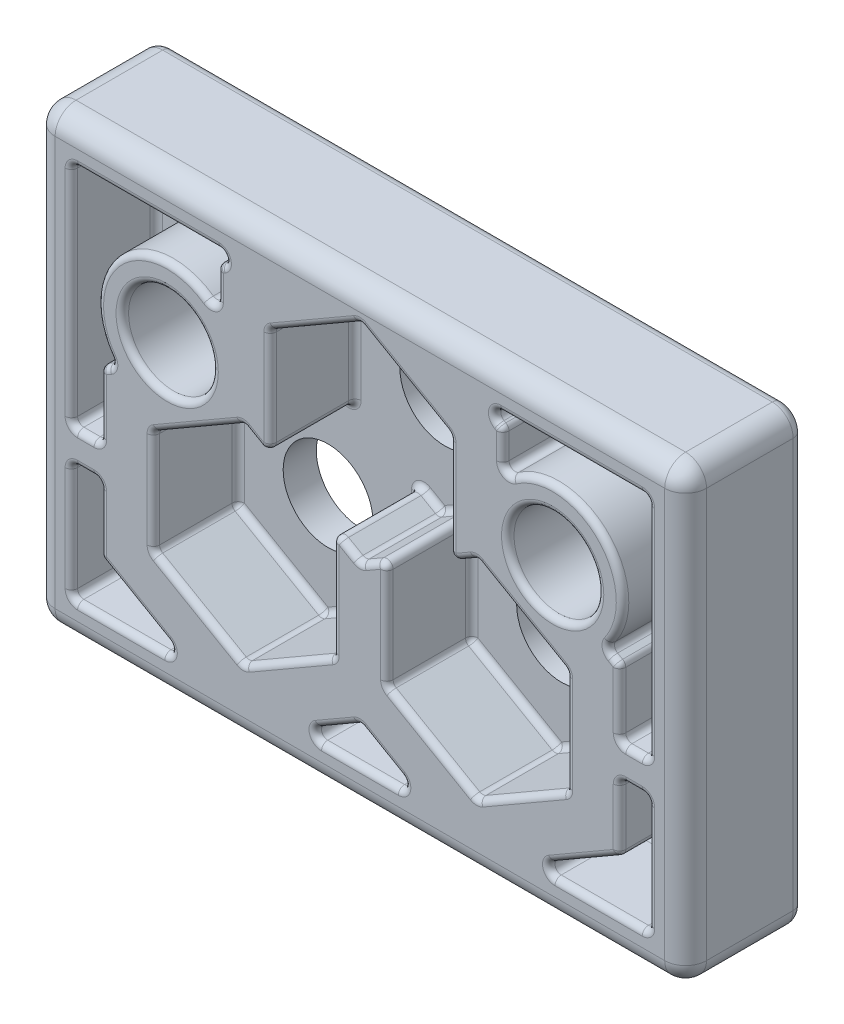
SolidWorks part; units mm, degrees
ref_plane "Front Plane" through (0, 0, 0) normal (0, 0, 1) x (1, 0, 0)
ref_plane "Top Plane" through (0, 0, 0) normal (0, 1, 0) x (1, 0, 0)
ref_plane "Right Plane" through (0, 0, 0) normal (1, 0, 0) x (0, 0, -1)
sketch "Sketch1" plane through (0, 0, 0) normal (0, 0, 1) x (1, 0, 0)
  line L0 (0, 10.795) -> (0, -10.795) construction
  line L1 (-15.5956, 10.795) -> (15.5956, 10.795)
  line L2 (-15.5956, 10.795) -> (-15.5956, -10.795)
  line L3 (-15.5956, -10.795) -> (15.5956, -10.795)
  line L4 (15.5956, 10.795) -> (15.5956, -10.795)
  line L5 (-15.5956, 10.795) -> (15.5956, -10.795) construction
  line L6 (-15.5956, -10.795) -> (15.5956, 10.795) construction
  line L7 (-5.5905, -2.6391) -> (5.5905, -2.6391) construction
  line L8 (-9.2291, 3.9218) -> (9.2291, 3.9218) construction
  circle A0 centre (0, 4.3713) radius 2.1488
  circle A1 centre (5.5905, -2.6391) radius 2.1488
  circle A2 centre (-5.5905, -2.6391) radius 2.1488
  circle A3 centre (-9.2291, 3.9218) radius 2.1488
  circle A4 centre (9.2291, 3.9218) radius 2.1488
  point P0 (0, 0)
  point P13 (0, -2.6391)
  point P17 (0, 3.9218)
  point P19 (0, 0)
  dimension "D6" = 4.2977
  dimension "D1" = 31.1912
  dimension "D2" = 21.59
  dimension "D3" = 8.1559
  dimension "D4" = 11.1811
  dimension "D5" = 6.4237
  dimension "D7" = 18.4582
  dimension "D8" = 6.8732
extrude "Boss-Extrude1" add sketch "Sketch1" along normal blind 5.6515
sketch "Sketch2" plane through (0, 0, 5.6515) normal (0, 0, 1) x (1, 0, 0)
  line L0 (-2.957, -9.017) -> (0, -7.3098)
  line L1 (-5.5905, -7.6045) -> (-1.2903, -5.1218)
  line L2 (-1.2903, -2.6391) -> (-1.2903, -0.1563)
  line L3 (-1.2903, -0.1563) -> (-5.5905, 2.3264)
  line L5 (-5.5905, 2.3264) -> (-9.8908, -0.1563)
  line L6 (-9.8908, -0.1563) -> (-9.8908, -5.1218)
  line L7 (-9.8908, -5.1218) -> (-5.5905, -7.6045)
  line L8 (0, -0.5941) -> (4.3002, 1.8886)
  line L9 (4.3002, 1.8886) -> (4.3002, 6.8541)
  line L10 (4.3002, 6.8541) -> (0, 9.3368)
  line L11 (0, 9.3368) -> (-4.3002, 6.8541)
  line L12 (-4.3002, 6.8541) -> (-4.3002, 1.8886)
  line L13 (-4.3002, 1.8886) -> (0, -0.5941)
  line L14 (5.5905, -7.6045) -> (9.8908, -5.1218)
  line L15 (9.8908, -5.1218) -> (9.8908, -0.1563)
  line L16 (9.8908, -0.1563) -> (5.5905, 2.3264)
  line L53 (5.5905, 2.3264) -> (1.2903, -0.1563)
  line L54 (1.2903, -0.1563) -> (1.2903, -5.1218)
  line L55 (1.2903, -5.1218) -> (5.5905, -7.6045)
  line L59 (-12.4308, 1.3101) -> (-12.4308, -6.5883)
  line L60 (-12.4308, -6.5883) -> (-8.2241, -9.017)
  line L61 (1.2903, -2.7821) -> (1.2927, -2.7808)
  line L63 (6.8402, 8.3205) -> (0, 12.2697)
  line L64 (0, 12.2697) -> (-6.8402, 8.3205)
  line L69 (-6.8402, 8.3205) -> (-6.8402, 6.2671)
  line L71 (8.2241, -9.017) -> (12.4308, -6.5883)
  line L72 (12.4308, -6.5883) -> (12.4308, 1.3101)
  line L73 (12.4308, 1.3101) -> (11.7408, 1.7085)
  line L74 (4.3002, 4.5144) -> (4.2979, 4.513)
  line L76 (0, -7.3098) -> (2.957, -9.017)
  line L77 (-4.3002, 1.8886) -> (-4.3002, 1.5814)
  line L78 (-1.2903, -0.1563) -> (-1.2903, 0.1508)
  line L79 (-1.2903, 0.1508) -> (-4.3002, 1.8886)
  line L80 (-4.3002, 1.5814) -> (-1.2903, -0.1563)
  line L81 (1.2903, -0.1563) -> (1.2903, 0.1508)
  line L82 (1.2903, 0.1508) -> (4.3002, 1.8886)
  line L83 (4.3002, 1.5814) -> (1.2903, -0.1563)
  line L84 (4.3002, 1.8886) -> (4.3002, 1.5814)
  line L85 (-13.8176, -1.8771) -> (-12.4308, -1.8771)
  line L86 (-13.8176, 9.017) -> (13.8176, 9.017)
  line L87 (-13.8176, 9.017) -> (-13.8176, -9.017)
  line L88 (-13.8176, -9.017) -> (-8.2241, -9.017)
  line L89 (13.8176, 9.017) -> (13.8176, -9.017)
  line L90 (-13.8176, 9.017) -> (-5.8761, 3.8346) construction
  line L91 (-13.8176, -9.017) -> (5.8824, 3.8387) construction
  line L92 (-12.4308, -1.8771) -> (-12.4308, -3.4011)
  line L93 (-12.4308, -3.4011) -> (-13.8176, -3.4011)
  line L94 (-13.8176, -3.4011) -> (-13.8176, -1.8771)
  line L95 (12.4308, -1.8771) -> (13.8176, -1.8771)
  line L96 (13.8176, -1.8771) -> (13.8176, -3.4011)
  line L97 (13.8176, -3.4011) -> (12.4308, -3.4011)
  line L98 (12.4308, -3.4011) -> (12.4308, -1.8771)
  line L99 (0, -3.5271) -> (6.8402, 0.4221) construction
  line L100 (12.4308, 1.3101) -> (5.5905, 5.2593) construction
  line L101 (6.8402, 6.2671) -> (6.8402, 8.3205)
  line L102 (6.8402, 0.4221) -> (6.8402, 8.3205) construction
  line L104 (5.8824, 3.8387) -> (13.8176, 9.017) construction
  line L105 (5.5905, -10.5375) -> (12.4308, -6.5883) construction
  line L106 (-1.2497, -6.5883) -> (5.5905, -10.5375) construction
  line L107 (8.2241, -9.017) -> (13.8176, -9.017)
  line L108 (-5.5905, -10.5375) -> (1.2497, -6.5883) construction
  line L109 (-12.4308, -6.5883) -> (-5.5905, -10.5375) construction
  line L110 (-2.957, -9.017) -> (2.957, -9.017)
  line L111 (-1.2497, 1.3101) -> (-1.2497, -6.5883) construction
  line L112 (1.2497, -6.5883) -> (1.2497, 1.3101) construction
  line L113 (-1.2903, -5.1218) -> (-1.2903, -2.6391)
  line L114 (-6.8402, 0.4221) -> (0, -3.5271) construction
  line L115 (-6.8402, 8.3205) -> (-6.8402, 0.4221) construction
  line L116 (-11.7408, 1.7085) -> (-12.4308, 1.3101)
  line L117 (-5.5905, 5.2593) -> (-12.4308, 1.3101) construction
  line L119 (1.2497, 1.3101) -> (-5.5905, 5.2593) construction
  line L120 (-5.8761, 3.8346) -> (13.8176, -9.017) construction
  line L121 (5.5905, 5.2593) -> (-1.2497, 1.3101) construction
  line L123 (-1.2903, -5.1218) -> (-1.2903, -0.1563) construction
  circle A0 centre (-5.5905, -2.6391) radius 4.3002 construction
  circle A1 centre (0, 4.3713) radius 4.3002 construction
  circle A2 centre (5.5905, -2.6391) radius 4.3002 construction
  circle A8 centre (-9.2291, 3.9218) radius 3.3477
  arc A9 (-6.8402, 6.2671) -> (-11.7408, 1.7085) centre (-9.2291, 3.9218) ccw
  circle A11 centre (9.2291, 3.9218) radius 3.3477
  arc A12 (11.7408, 1.7085) -> (6.8402, 6.2671) centre (9.2291, 3.9218) ccw
  point P31 (-2.0869, -0.1501)
  point P40 (-1.4822, -5.1155)
  point P46 (0, 0)
  point P49 (0, 0)
  point P60 (0, 0)
  point P69 (-1.4014, -1.668)
  point P72 (-1.2903, -2.5892)
  point P75 (-1.2903, -2.6391)
  point P83 (-5.8192, 3.9218)
  point P84 (-4.3002, -0.5941)
  dimension "D1" = 2.54
  dimension "D6" = 5.6159
  dimension "D7" = 1.1989
  dimension "D8" = 1.1989
  dimension "D2" = 8.6004
  dimension "D3" = 27.6352
  dimension "D4" = 18.034
  dimension "D5" = 1.524
extrude "Cut-Extrude3" cut sketch "Sketch2" against normal blind 4.064
fillet "Fillet1" radius 0.2997 114 edges at (-13.1242, -3.4011, 5.6515) (-11.0208, -9.017, 5.6515) (-1.4785, -8.1634, 5.6515) (1.4785, -8.1634, 5.6515) (13.8176, -6.209, 5.6515) (12.4308, -4.9947, 5.6515) (11.0208, -9.017, 5.6515) (9.7258, 9.017, 5.6515) (6.8402, 7.2938, 5.6515) (-4.3002, 4.2178, 5.6515) (2.1501, 8.0954, 5.6515) (4.9454, 1.9539, 5.6515) (9.8908, -2.6391, 5.6515) (3.4404, -6.3632, 5.6515) (0.6452, -0.2216, 5.6515) (-1.2903, -2.4855, 5.6515) (-7.7406, -6.3632, 5.6515) (-7.7406, 1.085, 5.6515) (-9.7258, 9.017, 5.6515) (-13.1242, -1.8771, 5.6515) (-12.0858, 1.5093, 5.6515) (-6.8402, 7.2938, 5.6515) (-8.2241, -9.017, 3.6195) (-10.3274, -7.8026, 5.6515) (-12.4308, -6.5883, 3.6195) (-12.4308, -3.4011, 3.6195) (-12.4308, -4.9947, 5.6515) (-13.8176, -3.4011, 3.6195) (-13.8176, -6.209, 5.6515) (-10.3274, -7.8026, 1.5875) (-11.0208, -9.017, 1.5875) (-13.8176, -6.209, 1.5875) (-13.1242, -3.4011, 1.5875) (-12.4308, -4.9947, 1.5875) (-2.957, -9.017, 3.6195) (2.957, -9.017, 3.6195) (0, -9.017, 5.6515) (1.4785, -8.1634, 1.5875) (0, -9.017, 1.5875) (-1.4785, -8.1634, 1.5875) (13.8176, -3.4011, 3.6195) (12.4308, -3.4011, 3.6195) (13.1242, -3.4011, 5.6515) (12.4308, -6.5883, 3.6195) (8.2241, -9.017, 3.6195) (12.4308, -4.9947, 1.5875) (13.1242, -3.4011, 1.5875) (13.8176, -6.209, 1.5875) (11.0208, -9.017, 1.5875) (10.3274, -7.8026, 1.5875) (12.4308, 1.3101, 3.6195) (12.4308, -0.2835, 5.6515) (13.8176, -1.8771, 3.6195) (13.8176, 9.017, 3.6195) (13.8176, 3.57, 5.6515) (6.8402, 8.3205, 3.6195) (6.8402, 7.2938, 1.5875) (9.7258, 9.017, 1.5875) (13.8176, 3.57, 1.5875) (13.1242, -1.8771, 1.5875) (12.4308, -0.2835, 1.5875) (12.0858, 1.5093, 1.5875) (6.8402, 6.2671, 3.6195) (11.5092, 6.3729, 1.5875) (11.7408, 1.7085, 3.6195) (11.5092, 6.3729, 5.6515) (-2.1501, 8.0954, 1.5875) (-2.1501, 8.0954, 5.6515) (4.3002, 1.5814, 3.6195) (4.3002, 6.8541, 3.6195) (4.3002, 4.2178, 5.6515) (9.8908, -0.1563, 3.6195) (7.7406, 1.085, 1.5875) (5.5905, 2.3264, 3.6195) (7.7406, 1.085, 5.6515) (9.8908, -5.1218, 3.6195) (1.2903, 0.1508, 3.6195) (1.2903, -2.4855, 1.5875) (1.2903, -5.1218, 3.6195) (1.2903, -2.4855, 5.6515) (-1.2903, 0.1508, 3.6195) (0, -0.5941, 3.6195) (-5.5905, -7.6045, 3.6195) (-3.4404, -6.3632, 1.5875) (-1.2903, -5.1218, 3.6195) (-3.4404, -6.3632, 5.6515) (-9.8908, -2.6391, 1.5875) (-9.8908, -5.1218, 3.6195) (-9.8908, -2.6391, 5.6515) (-4.3002, 1.5814, 3.6195) (-4.9454, 1.9539, 1.5875) (-5.5905, 2.3264, 3.6195) (-4.9454, 1.9539, 5.6515) (-13.8176, 9.017, 3.6195) (-6.8402, 8.3205, 3.6195) (-12.4308, -1.8771, 3.6195) (-12.4308, 1.3101, 3.6195) (-12.4308, -0.2835, 5.6515) (-11.7408, 1.7085, 3.6195) (-12.4308, -0.2835, 1.5875) (-13.8176, 3.57, 1.5875) (-6.2371, 8.6688, 1.5875) (-6.8402, 7.2938, 1.5875) (-11.5092, 6.3729, 1.5875) (0, -7.3098, 3.6195) (13.8176, -9.017, 3.6195) (11.3779, 3.9218, 5.6515) (2.1501, 8.0954, 1.5875) (4.9454, 1.9539, 1.5875) (3.4404, -6.3632, 1.5875) (0.6452, -0.2216, 1.5875) (-7.7406, -6.3632, 1.5875) (-7.7406, 1.085, 1.5875) (-7.0802, 3.9218, 5.6515)
fillet "Fillet2" radius 1.0008 8 edges at (15.5956, 10.795, 2.8258) (15.5956, 0, 5.6515) (15.5956, -10.795, 2.8258) (0, -10.795, 5.6515) (-15.5956, -10.795, 2.8258) (-15.5956, 0, 5.6515) (0, 10.795, 5.6515) (-15.5956, 10.795, 2.8258)
fillet "Fillet3" radius 0.5004 8 edges at (-15.3025, 10.5019, 0) (0, 10.795, 0) (15.3025, 10.5019, 0) (15.5956, 0, 0) (15.3025, -10.5019, 0) (0, -10.795, 0) (-15.3025, -10.5019, 0) (-15.5956, 0, 0)
